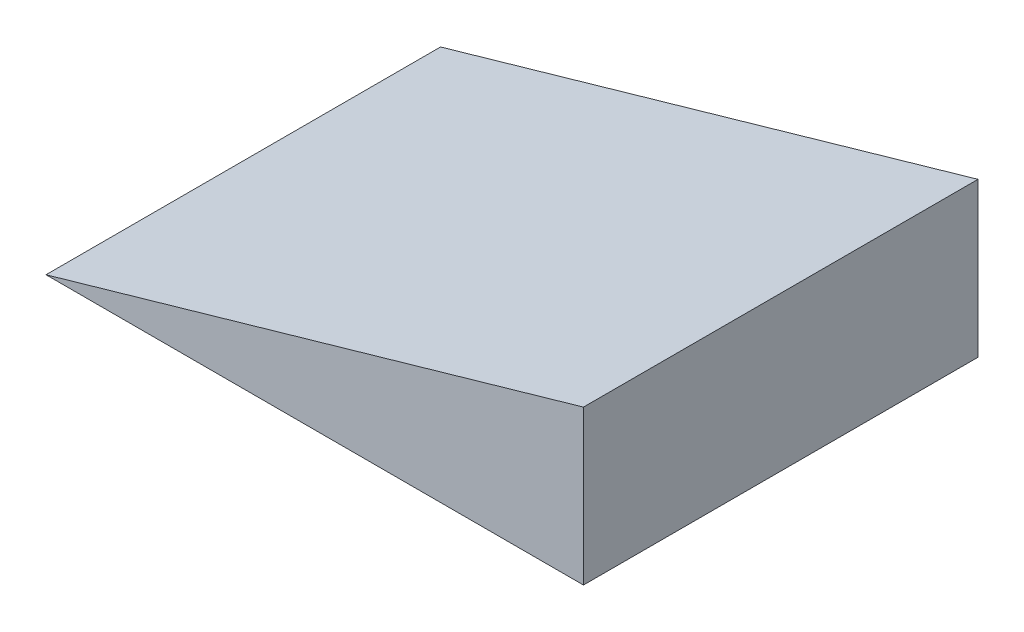
SolidWorks part; units mm, degrees
material "Maple"
ref_plane "Front Plane" through (0, 0, 0) normal (0, 0, 1) x (1, 0, 0)
ref_plane "Top Plane" through (0, 0, 0) normal (0, 1, 0) x (1, 0, 0)
ref_plane "Right Plane" through (0, 0, 0) normal (1, 0, 0) x (0, 0, -1)
sketch "Sketch1" plane through (0, 0, 0) normal (0, 0, 1) x (1, 0, 0)
  line L0 (0, 0) -> (0, 158.75)
  line L1 (0, 158.75) -> (-553.627, 0)
  line L2 (-553.627, 0) -> (0, 0)
  dimension "D1" = 16
  dimension "D2" = 158.75
extrude "Boss-Extrude1" add sketch "Sketch1" against normal blind 406.4
